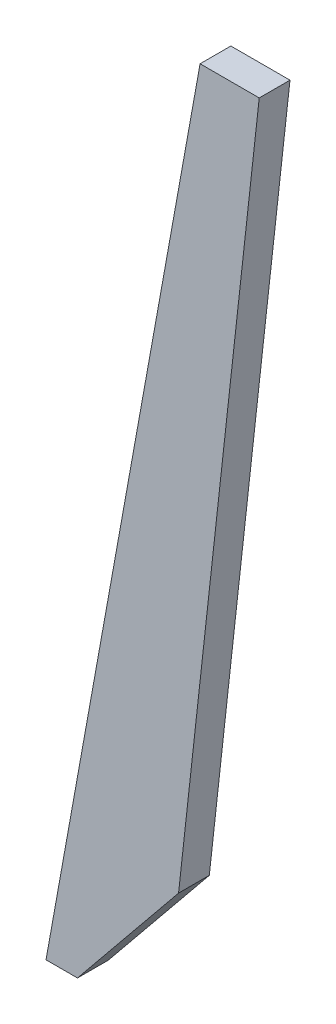
SolidWorks part; units mm, degrees
ref_plane "Front Plane" through (0, 0, 0) normal (0, 0, 1) x (1, 0, 0)
ref_plane "Top Plane" through (0, 0, 0) normal (0, 1, 0) x (1, 0, 0)
ref_plane "Right Plane" through (0, 0, 0) normal (1, 0, 0) x (0, 0, -1)
sketch "Sketch3" plane through (0, 0, 0) normal (0, 0, 1) x (1, 0, 0)
  line L0 (400.5772, 416) -> (361.2334, 60.4896)
  line L1 (311.9448, 0) -> (296.5972, 0)
  line L3 (296.5972, 0) -> (371.7349, 416)
  line L5 (371.7349, 416) -> (400.5772, 416)
  line L6 (329.2398, 180.7256) -> (374.5398, 180.7256) construction
  line L7 (311.9448, 0) -> (361.2334, 60.4896)
  point P1 (360.3101, 37.8497)
  point P9 (359.7812, 44.8663)
  point P10 (323.2398, 0)
  dimension "D1" = 45.3
extrude "Boss-Extrude1" add sketch "Sketch3" along normal blind 15
